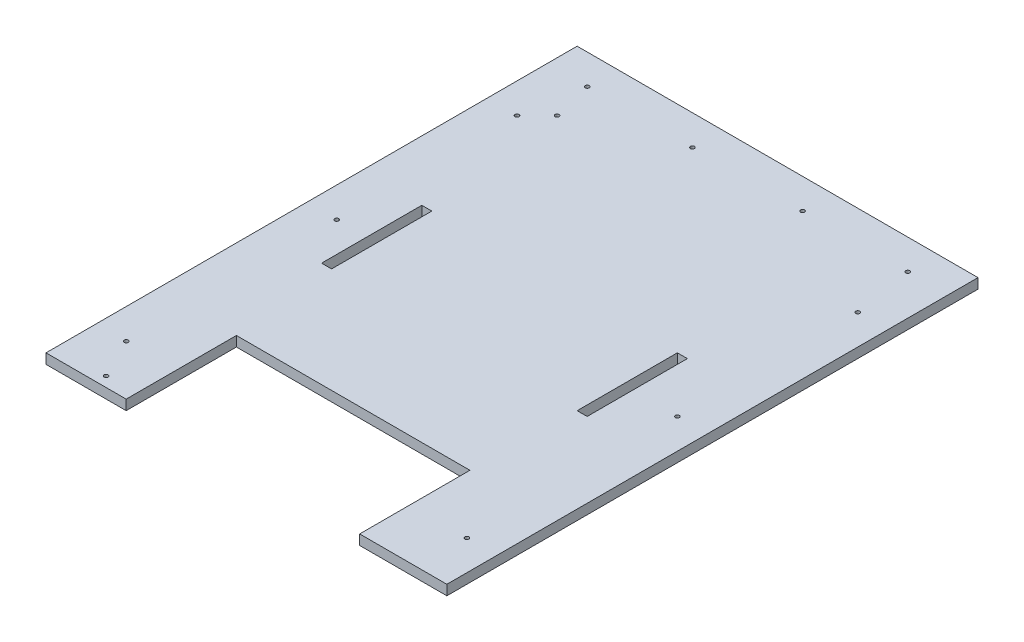
SolidWorks part; units mm, degrees
ref_plane "Front Plane" through (0, 0, 0) normal (0, 0, 1) x (1, 0, 0)
ref_plane "Top Plane" through (0, 0, 0) normal (0, 1, 0) x (1, 0, 0)
ref_plane "Right Plane" through (0, 0, 0) normal (1, 0, 0) x (0, 0, -1)
sketch "Sketch1" plane through (0, 0, 0) normal (0, 1, 0) x (1, 0, 0)
  line L0 (-200, 530) -> (-200, 0)
  line L1 (200, 530) -> (200, 0)
  line L2 (-120, 0) -> (-120, 110)
  line L3 (-120, 110) -> (113, 110)
  line L4 (113, 110) -> (113, 0)
  line L5 (-130, 315) -> (-130, 215)
  line L6 (115, 315) -> (115, 215)
  line L9 (-200, 530) -> (200, 530)
  line L10 (-130, 215) -> (-140, 215)
  line L11 (-200, 0) -> (-120, 0)
  line L12 (-140, 215) -> (-140, 315)
  line L13 (-140, 315) -> (-130, 315)
  line L16 (115, 215) -> (125, 215)
  line L17 (125, 215) -> (125, 315)
  line L18 (125, 315) -> (115, 315)
  line L32 (113, 0) -> (200, 0)
  circle A0 centre (-160, 500) radius 2
  circle A1 centre (-55, 500) radius 2
  circle A2 centre (55, 500) radius 2
  circle A3 centre (160, 500) radius 2
  circle A4 centre (-170, 50) radius 2
  circle A5 centre (-170, 260) radius 2
  circle A6 centre (-170, 440) radius 2
  circle A7 centre (170, 440) radius 2
  circle A8 centre (170, 260) radius 2
  circle A9 centre (170, 50) radius 2
  circle A10 centre (-150, 10) radius 2
  circle A11 centre (-150, 460) radius 2
extrude "Boss-Extrude1" add sketch "Sketch1" along normal blind 10
